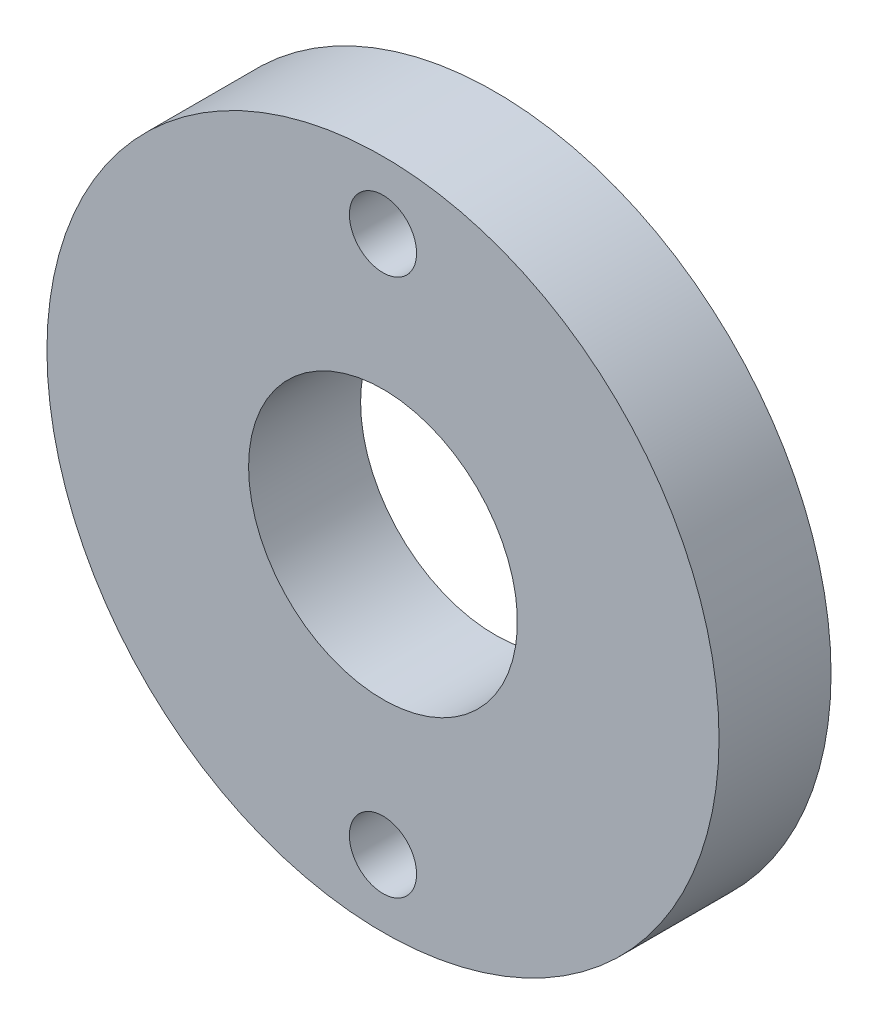
SolidWorks part; units mm, degrees
other "Markup1"
sketch "Sketch17" plane through (198.0015, -131.0823, 17.4914) normal (-0.589, 0.0933, 0.8027) x (0.8081, 0.0619, 0.5858)
sketch "Sketch20" plane through (244.3015, -133.5737, 0) normal (-0.589, 0.0933, 0.8027) x (0.8081, 0.0619, 0.5858)
material "AISI 304"
ref_plane "Front Plane" through (0, 0, 0) normal (0, 0, 1) x (1, 0, 0)
ref_plane "Top Plane" through (0, 0, 0) normal (0, 1, 0) x (1, 0, 0)
ref_plane "Right Plane" through (0, 0, 0) normal (1, 0, 0) x (0, 0, -1)
sketch "Sketch19" plane through (259.3015, 0, 0) normal (0, 0, -1) x (-1, 0, 0)
  circle A0 centre (0, -148.5737) radius 15
  circle A1 centre (0, -148.5737) radius 6
  circle A2 centre (0, -136.5737) radius 1.5
  circle A3 centre (0, -160.5737) radius 1.5
  dimension "D1" = 3
  dimension "D2" = 30
  dimension "D3" = 12
  dimension "D4" = 3
extrude "Boss-Extrude1" add sketch "Sketch19" along normal blind 5
